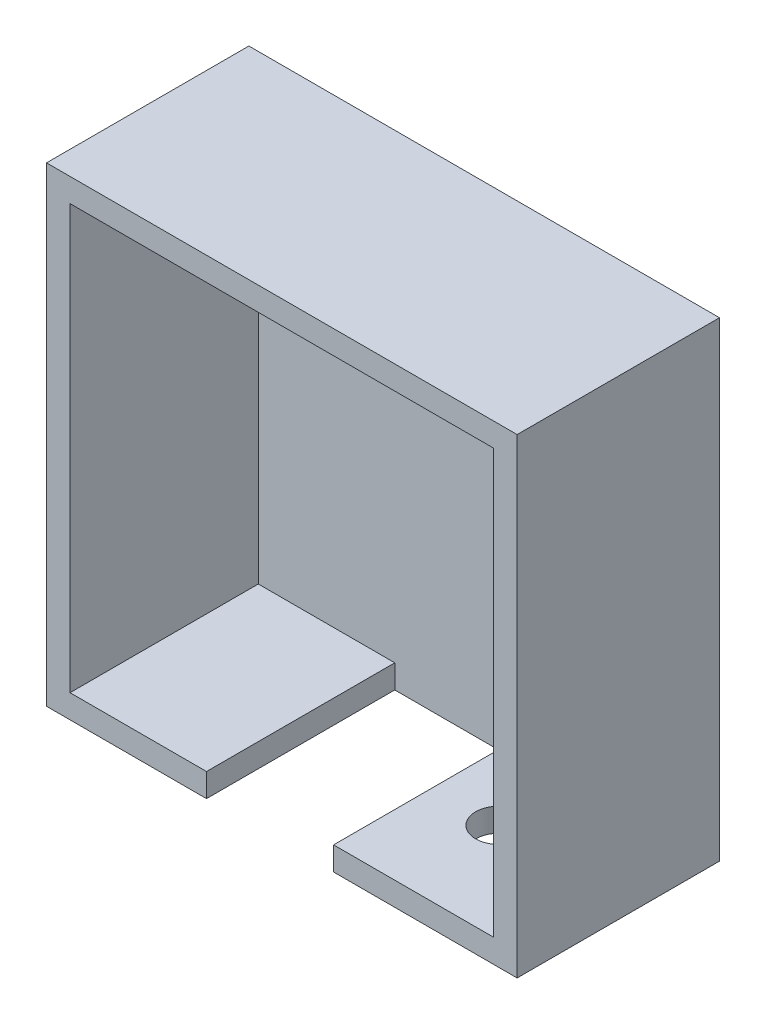
SolidWorks part; units mm, degrees
other "Markup1"
sketch "Sketch4" plane through (150, -150, 43) normal (0.0905, -0.8723, 0.4805) x (0.9874, 0.1415, 0.071)
ref_plane "Front Plane" through (0, 0, 0) normal (0, 0, 1) x (1, 0, 0)
ref_plane "Top Plane" through (0, 0, 0) normal (0, 1, 0) x (1, 0, 0)
ref_plane "Right Plane" through (0, 0, 0) normal (1, 0, 0) x (0, 0, -1)
sketch "Sketch1" plane through (0, 0, 0) normal (0, 0, 1) x (1, 0, 0)
  line L1 (0, 0) -> (100, 0)
  line L2 (0, 0) -> (0, -100)
  line L3 (0, -100) -> (100, -100)
  line L4 (100, 0) -> (100, -100)
  dimension "D1" = 100
  dimension "D2" = 100
extrude "Boss-Extrude1" add sketch "Sketch1" along normal blind 3
sketch "Sketch2" plane through (0, 0, 3) normal (0, 0, 1) x (1, 0, 0)
  line L0 (0, -100) -> (100, -100) construction
  line L1 (0, 0) -> (100, 0)
  line L2 (0, 0) -> (0, -6.0759)
  line L3 (5, -5) -> (95, -5)
  line L4 (100, 0) -> (100, -5)
  line L10 (100, -5) -> (100, -100)
  line L12 (95, -5) -> (95, -95)
  line L13 (5, -95) -> (34, -95)
  line L15 (0, -100) -> (34, -100)
  line L16 (34, -95) -> (34, -100)
  line L17 (0, 0) -> (0, -100) construction
  line L18 (100, -100) -> (100, 0) construction
  line L19 (100, 0) -> (0, 0) construction
  line L20 (61, -95) -> (95, -95)
  line L22 (0, -6.0759) -> (0, -100)
  line L24 (5, -5) -> (5, -95)
  line L25 (61, -95) -> (61, -100)
  line L26 (61, -100) -> (100, -100)
  dimension "D1" = 34
  dimension "D2" = 5
  dimension "D3" = 5
  dimension "D4" = 5
  dimension "D5" = 5
  dimension "D6" = 5
  dimension "D7" = 34
extrude "Boss-Extrude2" add sketch "Sketch2" along normal blind 40
sketch "Sketch3" plane through (0, -100, 0) normal (0, -1, 0) x (1, 0, 0)
  line L0 (0, 43) -> (0, 0) construction
  circle A0 centre (75, 21.8065) radius 5
  dimension "D1" = 10
  dimension "D2" = 75
extrude "Cut-Extrude1" cut sketch "Sketch3" against normal blind 40 contours A0
